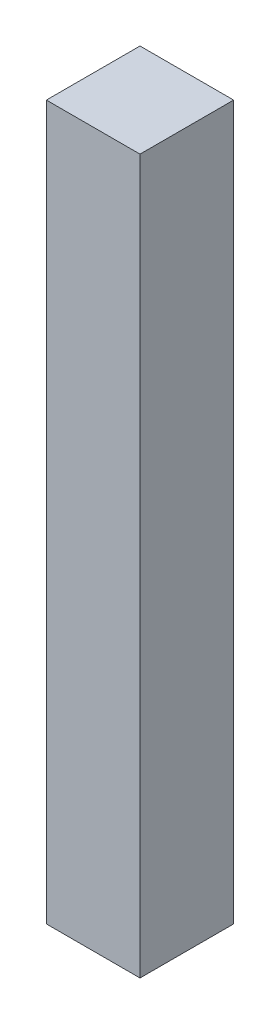
SolidWorks part; units mm, degrees
ref_plane "Front Plane" through (0, 0, 0) normal (0, 0, 1) x (1, 0, 0)
ref_plane "Top Plane" through (0, 0, 0) normal (0, 1, 0) x (1, 0, 0)
ref_plane "Right Plane" through (0, 0, 0) normal (1, 0, 0) x (0, 0, -1)
sketch "Sketch1" plane through (0, 0, 0) normal (0, 1, 0) x (1, 0, 0)
  line L1 (-20, -20) -> (20, -20)
  line L2 (-20, -20) -> (-20, 20)
  line L3 (-20, 20) -> (20, 20)
  line L4 (20, -20) -> (20, 20)
  line L5 (-20, -20) -> (20, 20) construction
  line L6 (-20, 20) -> (20, -20) construction
  point P0 (0, 0)
  dimension "D1" = 40
extrude "Boss-Extrude1" add sketch "Sketch1" along normal blind 304.8
